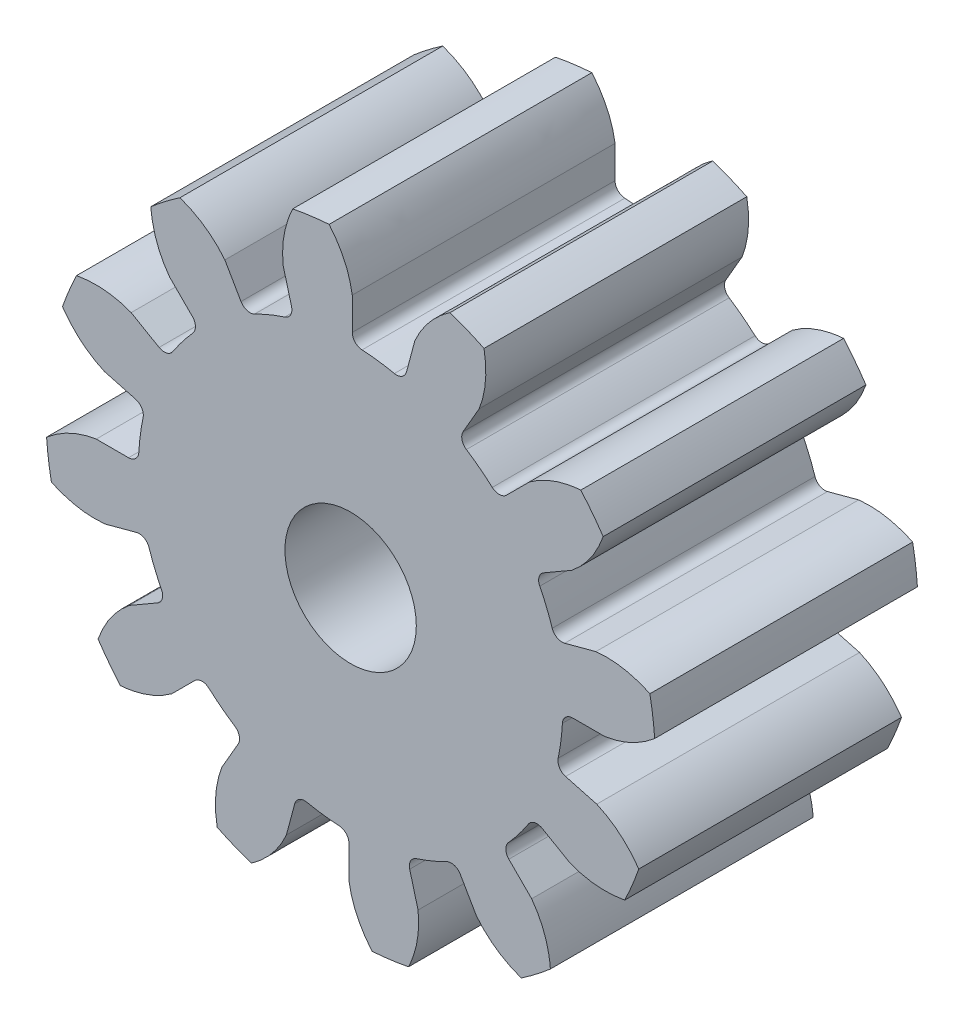
SolidWorks part; units mm, degrees
ref_plane "Front" through (0, 0, 0) normal (0, 0, 1) x (1, 0, 0)
ref_plane "Top" through (0, 0, 0) normal (0, 1, 0) x (1, 0, 0)
ref_plane "Right" through (0, 0, 0) normal (1, 0, 0) x (0, 0, -1)
sketch "Sketch1" plane through (0, 0, 0) normal (0, 0, 1) x (1, 0, 0)
  line L0 (-152.4, 0) -> (152.4, 0) construction
  circle A0 centre (0, 0) radius 7.366
  circle A1 centre (0, 0) radius 6.35 construction
  circle A3 centre (0, 0) radius 5.1255 construction
  dimension "D1" = 1.2245
  dimension "OD" = 14.732
  dimension "Ptich Dia" = 12.7
  dimension "D2" = 2.2405
  dimension "Root Dia" = 10.251
  dimension "D3" = 1.016
  dimension "Number of Teeth" = 304.8
extrude "Boss-Extrude1" add sketch "Sketch1" against normal blind 6.35
sketch "Sketch2" plane through (0, 0, 0) normal (1, 0, 0) x (0, 0, -1)
  line L0 (6.35, 0) -> (14.2875, 0)
  line L1 (6.35, 0) -> (6.35, 4.7625)
  line L2 (6.35, 4.7625) -> (14.2875, 4.7625)
  line L3 (14.2875, 4.7625) -> (14.2875, 0)
  point P5 (14.2875, -4.7625)
  point P6 (0, -7.366)
  point P7 (6.35, -7.366)
  point P9 (0, 7.366)
  dimension "Face Wd" = 6.35
  dimension "B Hub Dia" = 9.525
  dimension "D O'all Lg." = 14.2875
sketch "Sketch3" plane through (0, 0, 0) normal (0, 0, 1) x (1, 0, 0)
  line L0 (0, 0) -> (0, 7.366) construction
  line L1 (-1.5393, 5.9519) -> (0, 6.35)
  line L2 (-9.5921, 6.35) -> (9.5921, 6.35) construction
  line L3 (-9.2865, 3.9483) -> (9.2865, 8.7517) construction
  line L4 (-1.5393, 5.9519) -> (0, 0) construction
  line L5 (-3.8025, 4.8307) -> (0, 0) construction
  line L6 (-3.8025, 4.8307) -> (-0.5543, 7.3875) construction
  line L7 (-1.0733, 6.0533) -> (0, 0) construction
  line L8 (-1.0733, 6.0533) -> (0.0225, 6.2476) construction
  arc A0 (-1.5393, 5.9519) -> (-3.8025, 4.8307) centre (0, 0) ccw
  circle A1 centre (0, 0) radius 6.35 construction
  circle A2 centre (0, 0) radius 6.1477 construction
  arc A3 (-1.5393, 5.9519) -> (-1.0733, 6.0533) centre (0, 0) cw
  circle A4 centre (0, 0) radius 7.366 construction
  point P6 (0, 6.35)
  dimension "D1" = 1.5899
  dimension "Pressure Angle" = 14.5
  dimension "D2" = 2.5439
  dimension "D3" = 4.1338
  dimension "D4" = 0.477
  dimension "D5" = 1.1129
sketch "Sketch4" plane through (0, 0, 0) normal (0, 0, 1) x (1, 0, 0)
  line L0 (0, 0) -> (0.8218, 6.2418) construction
  line L1 (0.04, 6.1476) -> (0.04, 5.1254)
  line L2 (0, 6.35) -> (1.6435, 6.1336) construction
  line L3 (1.5525, 5.9485) -> (1.2879, 4.9611)
  line L4 (0.04, 5.1254) -> (0, 0) construction
  line L5 (0, 0) -> (0, 7.366) construction
  line L6 (-3.8025, 4.8307) -> (-0.5543, 7.3875) construction
  line L7 (-3.8025, 4.8307) -> (-0.5543, 7.3875) construction
  arc A0 (1.2879, 4.9611) -> (0.04, 5.1254) centre (0, 0) ccw
  arc A1 (0, 6.35) -> (1.6435, 6.1336) centre (0, 0) cw construction
  circle A2 centre (0, 0) radius 6.35 construction
  circle A3 centre (0, 0) radius 6.1477 construction
  circle A4 centre (0, 0) radius 5.1255 construction
  arc A5 (2.4475, 6.9923) -> (-0.5543, 7.3875) centre (0, 0) ccw
  spline S0 degree 2 poles (-0.5543, 7.3875) (-0.0642, 6.8316) (0.04, 6.1476) knots 0 0 0 1 1 1
  spline S1 degree 2 poles (2.4475, 6.9923) (1.8302, 6.5822) (1.5525, 5.9485) knots 0 0 0 1 1 1
  dimension "D1" = 1.6624
extrude "Cut-Extrude1" cut sketch "Sketch4" against normal through all
fillet "Fillet1" radius 0.2494 2 edges at (1.2879, 4.9611, -3.175) (0.04, 5.1254, -3.175)
pattern_circular "CirPattern1" count 12 over 360 about axis through (0, 0, -6.35) along (0, 0, 1) of "Cut-Extrude1", "Fillet1"
sketch "Sketch5" plane through (0, 0, 0) normal (0, 0, 1) x (1, 0, 0)
  circle A0 centre (0, 0) radius 1.5875
  circle A1 centre (0, 0) radius 1.5875 construction
  dimension "Bore Min" = 3.175
  dimension "Bore Max" = 3.175
extrude "Cut-Extrude2" cut sketch "Sketch5" against normal through all
sketch "Pitch Dia" plane through (0, 0, 0) normal (0, 0, 1) x (1, 0, 0)
  circle A0 centre (0, 0) radius 6.35 construction
  circle A1 centre (0, 0) radius 6.35
equation "\"D1@Boss-Extrude1\" = \"Face Wd@Sketch2\""
equation "\"D2@Sketch3\" = \"D1@Sketch3\"*1.6"
equation "\"D3@Sketch3\" = \"D1@Sketch3\"+\"D2@Sketch3\""
equation "\"D4@Sketch3\" = \"D1@Sketch3\"*.3"
equation "\"D5@Sketch3\" = \"D1@Sketch3\"-\"D4@Sketch3\""
equation "\"D1@Sketch4\" = 1.5708/(\"Number of Teeth@Sketch1\"/\"Ptich Dia@Sketch1\")"
equation "\"D1@Chamfer1\" = \"B Hub Dia@Sketch2\"*.025"
equation "\"D1@CirPattern1\" = \"Number of Teeth@Sketch1\""
equation "\"D1@Fillet1\" = \"D1@Sketch4\"*.15"
equation "\"D1@Fillet2\" = \"OD@Sketch1\"*.01"
equation "\"D1@Sketch1\" = 1.157/(\"Number of Teeth@Sketch1\"/\"Ptich Dia@Sketch1\")"
